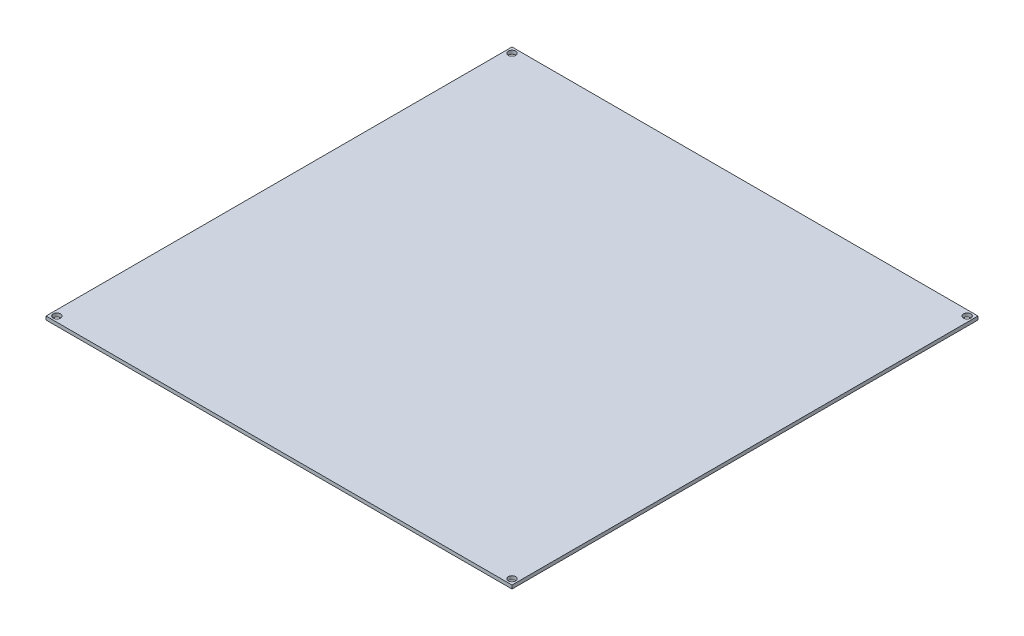
SolidWorks part; units mm, degrees
material "PE High Density"
ref_plane "Front Plane" through (0, 0, 0) normal (0, 0, 1) x (1, 0, 0)
ref_plane "Top Plane" through (0, 0, 0) normal (0, 1, 0) x (1, 0, 0)
ref_plane "Right Plane" through (0, 0, 0) normal (1, 0, 0) x (0, 0, -1)
sketch "Sketch1" plane through (0, 0, 0) normal (0, 1, 0) x (1, 0, 0)
  line L1 (0, 0) -> (214, 0)
  line L2 (0, 0) -> (0, 214)
  line L3 (0, 214) -> (214, 214)
  line L4 (214, 0) -> (214, 214)
  dimension "D1" = 214
  dimension "D2" = 214
extrude "Boss-Extrude1" add sketch "Sketch1" along normal blind 1.6
hole_wizard "Ø3.4 (3.4) Diameter Hole1" positions "Sketch3" profile "Sketch2" hole size "Ø3.4" standard "DIN" end condition through all
sketch "Sketch3" plane through (0, 1.6, 0) normal (0, 1, 0) x (1, 0, 0)
  line L0 (107, 214) -> (107, 0) construction
  line L1 (214, 214) -> (0, 214) construction
  line L2 (0, 0) -> (214, 0) construction
  line L4 (0, 107) -> (214, 107) construction
  line L5 (0, 214) -> (0, 0) construction
  line L6 (214, 0) -> (214, 214) construction
  point P0 (2.5, 211.5)
  point P2 (211.5, 211.5)
  point P4 (211.5, 2.5)
  point P6 (2.5, 2.5)
  dimension "D1" = 209
  dimension "D2" = 209
sketch "Sketch2" plane through (2.5, 1.6, -211.5) normal (1, 0, 0) x (0, 0, 1)
  line L0 (0, 0) -> (0, 1.6)
  line L1 (0, 1.6) -> (1.7, 1.6)
  line L2 (1.7, 1.6) -> (1.7, 0)
  line L5 (1.7, 0) -> (0, 0)
  line L11 (0, -6.35) -> (0, 107.95) construction
  dimension "Thru Hole Dia." = 3.4
  dimension "Thru Hole Depth" = 1.6
